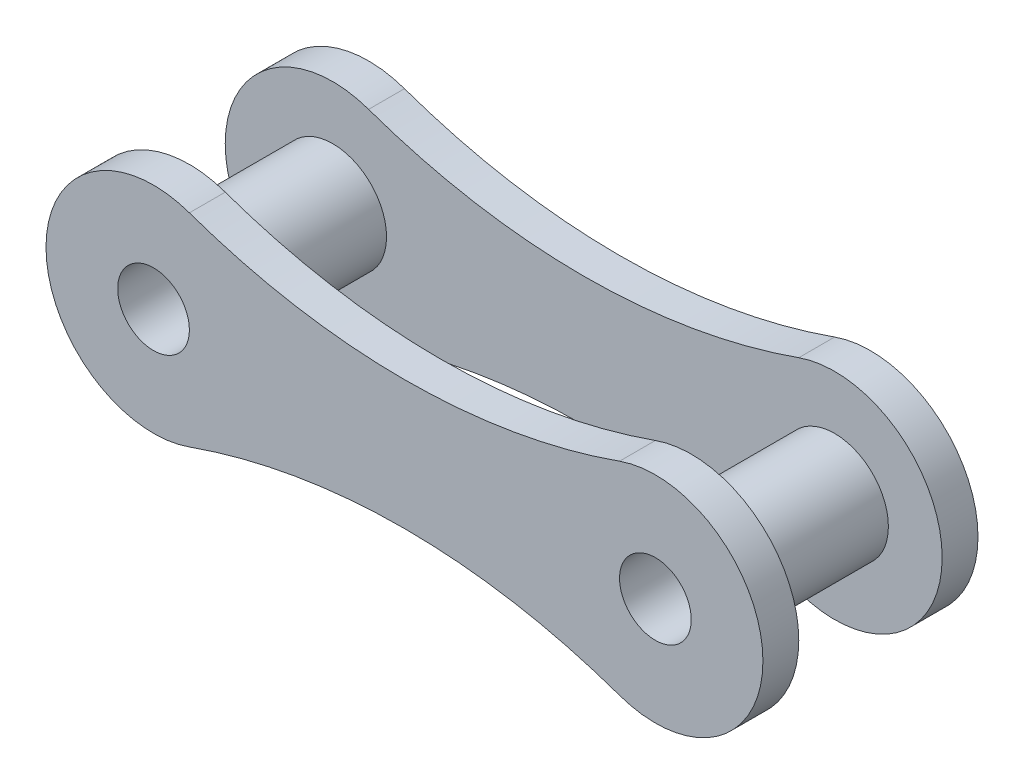
SolidWorks part; units mm, degrees
ref_plane "Front Plane" through (0, 0, 0) normal (0, 0, 1) x (1, 0, 0)
ref_plane "Top Plane" through (0, 0, 0) normal (0, 1, 0) x (1, 0, 0)
ref_plane "Right Plane" through (0, 0, 0) normal (1, 0, 0) x (0, 0, -1)
sketch "Sketch1" plane through (0, 0, 0) normal (0, 0, 1) x (1, 0, 0)
  line L0 (74.6129, 0) -> (-64.3109, 0) construction
  circle A0 centre (-7, 0) radius 1
  circle A1 centre (-7, 0) radius 3
  circle A2 centre (7, 0) radius 1
  circle A3 centre (7, 0) radius 3
  arc A4 (-6, 2.8284) -> (6, 2.8284) centre (0, 19.799) ccw
  arc A5 (6, -2.8284) -> (-6, -2.8284) centre (0, -19.799) ccw
  dimension "D1" = 6
  dimension "D2" = 2
  dimension "D3" = 7
  dimension "D4" = 7
extrude "Boss-Extrude1" add sketch "Sketch1" along normal blind 1 contours L0 A3 A4 A1 | L0 A1 A0 | L0 A3 A2 | A3 L0 A2 | A3 L0 A1 A5 | A1 L0 A0
sketch "Sketch2" plane through (0, 0, 1) normal (0, 0, 1) x (1, 0, 0)
  circle A0 centre (-7, 0) radius 1.5
  circle A1 centre (7, 0) radius 1.5
  circle A2 centre (-7, 0) radius 1
  circle A3 centre (7, 0) radius 1
  circle A4 centre (7, 0) radius 1 construction
  circle A5 centre (-7, 0) radius 1 construction
  dimension "D1" = 3
extrude "Boss-Extrude2" add sketch "Sketch2" along normal blind 5
ref_plane "Plane1" through (0, 0, 3) normal (0, 0, 1) x (1, 0, 0)
mirror "Mirror1" about plane through (0, 0, 3) normal (0, 0, 1) of "Boss-Extrude1"
